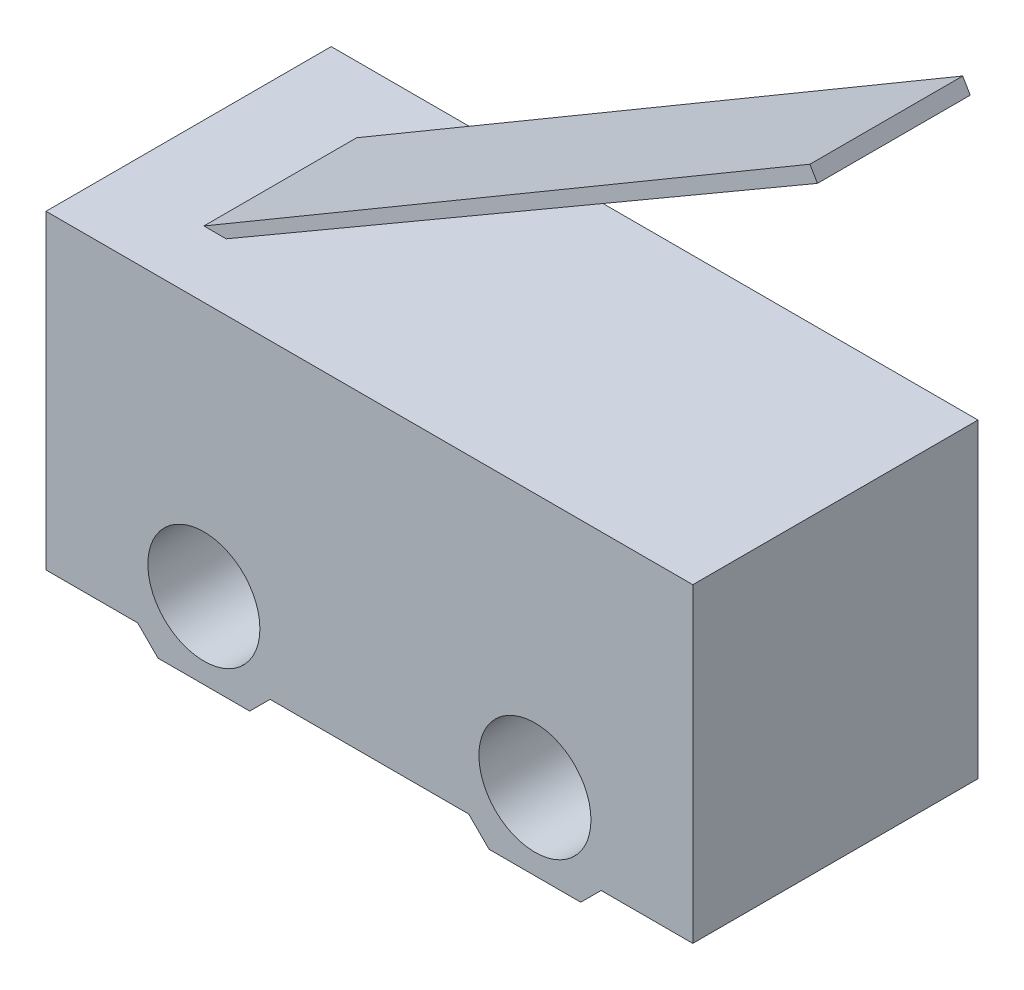
SolidWorks part; units mm, degrees
ref_plane "前视基准面" through (0, 0, 0) normal (0, 0, 1) x (1, 0, 0)
ref_plane "上视基准面" through (0, 0, 0) normal (0, 1, 0) x (1, 0, 0)
ref_plane "右视基准面" through (0, 0, 0) normal (1, 0, 0) x (0, 0, -1)
sketch "草图1" plane through (0, 0, 0) normal (0, 0, 1) x (1, 0, 0)
  line L0 (2.2, 0) -> (4, 0)
  line L1 (12.7, 0) -> (12.7, 6.5)
  line L2 (12.7, 6.5) -> (0, 6.5)
  line L3 (0, 6.5) -> (0, 0)
  line L4 (0, 0.4) -> (1.8, 0.4)
  line L5 (1.8, 0.4) -> (2.2, 0)
  line L6 (4.4, 0.4) -> (4, 0)
  line L7 (10.9, 0.4) -> (10.5, 0)
  line L8 (8.3, 0.4) -> (8.7, 0)
  line L9 (4.4, 0.4) -> (8.3, 0.4)
  line L10 (8.7, 0) -> (10.5, 0)
  line L11 (10.9, 0.4) -> (12.7, 0.4)
  line L12 (2, 6.5) -> (14.7, 13.5)
  line L13 (2, 6.5) -> (2.5179, 6.5)
  line L14 (2.5179, 6.5) -> (14.8207, 13.2811)
  line L15 (14.8207, 13.2811) -> (14.7, 13.5)
  circle A0 centre (3.1, 1.5) radius 1.1
  circle A2 centre (9.6, 1.5) radius 1.1
  dimension "D4" = 2.2
  dimension "D5" = 1.8
  dimension "D1" = 6.5
  dimension "D2" = 12.7
  dimension "D3" = 0.4
  dimension "D6" = 3.1
  dimension "D7" = 1.8
  dimension "D8" = 1.1
  dimension "D9" = 2
  dimension "D10" = 45
  dimension "D11" = 45
  dimension "D12" = 13.5
  dimension "D13" = 2
  dimension "D14" = 2
  dimension "D15" = 0.25
extrude "凸台-拉伸1" add sketch "草图1" along normal blind 5.6 contours L7 L11 L1 L2 L3 L4 L5 L0 L6 L9 L8 L10 A2 A0
ref_plane "基准面1" through (0, 0, 2.8) normal (0, 0, 1) x (1, 0, 0)
sketch "草图3" plane through (0, 0, 2.8) normal (0, 0, 1) x (1, 0, 0)
  line L1 (1.8, 6.5) -> (13.7, 13.5)
  line L2 (12.7, 6.5) -> (0, 6.5) construction
  line L3 (8.7, 0) -> (10.5, 0) construction
  line L4 (12.7, 0.4) -> (12.7, 6.5) construction
  line L5 (0, 6.5) -> (0, 0.4) construction
  line L6 (2.2383, 6.5) -> (13.8483, 13.2479)
  line L7 (13.8483, 13.2479) -> (13.7, 13.5)
  line L8 (2.2383, 6.5) -> (1.8, 6.5)
  dimension "D1" = 13.5
  dimension "D2" = 1
  dimension "D3" = 1.8
  dimension "D4" = 0.3
extrude "凸台-拉伸2" add sketch "草图3" along normal mid plane 3
